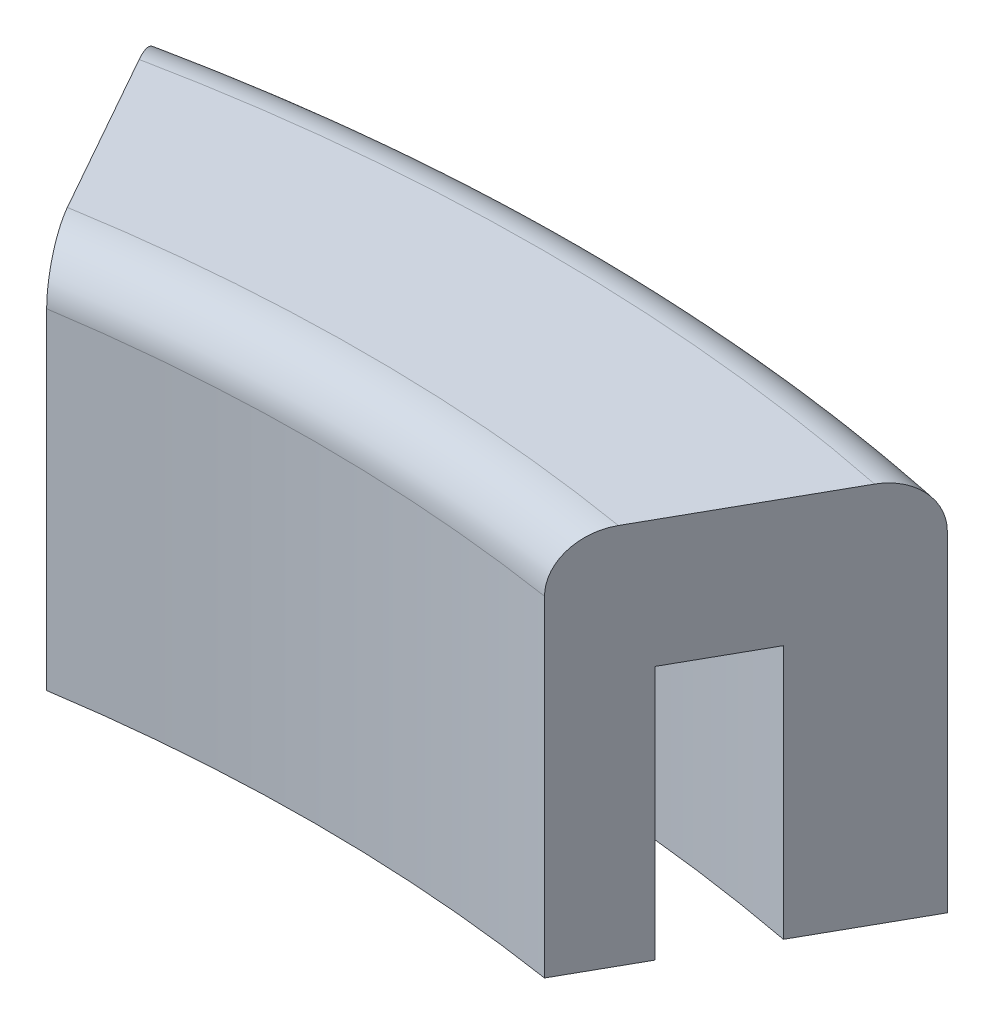
SolidWorks part; units mm, degrees
ref_plane "Front Plane" through (0, 0, 0) normal (0, 0, 1) x (1, 0, 0)
ref_plane "Top Plane" through (0, 0, 0) normal (0, 1, 0) x (1, 0, 0)
ref_plane "Right Plane" through (0, 0, 0) normal (1, 0, 0) x (0, 0, -1)
sketch "Sketch1" plane through (0, 0, 0) normal (0, 1, 0) x (1, 0, 0)
  line L0 (12.4292, 80.3241) -> (19.6669, 93.1975)
  line L1 (-12.4292, 80.3241) -> (-19.6669, 93.1975)
  line L2 (0, 0) -> (0, 95.25) construction
  arc A0 (-19.6669, 93.1975) -> (19.6669, 93.1975) centre (0, 0) cw
  arc A1 (-12.4292, 80.3241) -> (12.4292, 80.3241) centre (0, 0) cw
  dimension "D1" = 95.25
  dimension "D2" = 81.28
extrude "Boss-Extrude1" add sketch "Sketch1" along normal blind 19.05
sketch "Sketch3" plane through (0, 0, 0) normal (0, -1, 0) x (1, 0, 0)
  line L0 (-14.417, -83.8598) -> (-16.722, -87.9596)
  line L1 (16.722, -87.9596) -> (14.417, -83.8598)
  line L2 (12.4292, -80.3241) -> (19.6669, -93.1975) construction
  line L3 (-19.6669, -93.1975) -> (-12.4292, -80.3241) construction
  arc A0 (-16.722, -87.9596) -> (16.722, -87.9596) centre (0, 0) ccw
  arc A1 (-14.417, -83.8598) -> (14.417, -83.8598) centre (0, 0) ccw
  dimension "D1" = 89.535
  dimension "D2" = 85.09
extrude "Cut-Extrude1" cut sketch "Sketch3" against normal blind 12.7
fillet "Fillet1" radius 2.54 2 edges at (0, 19.05, -81.28) (0, 19.05, -95.25)
